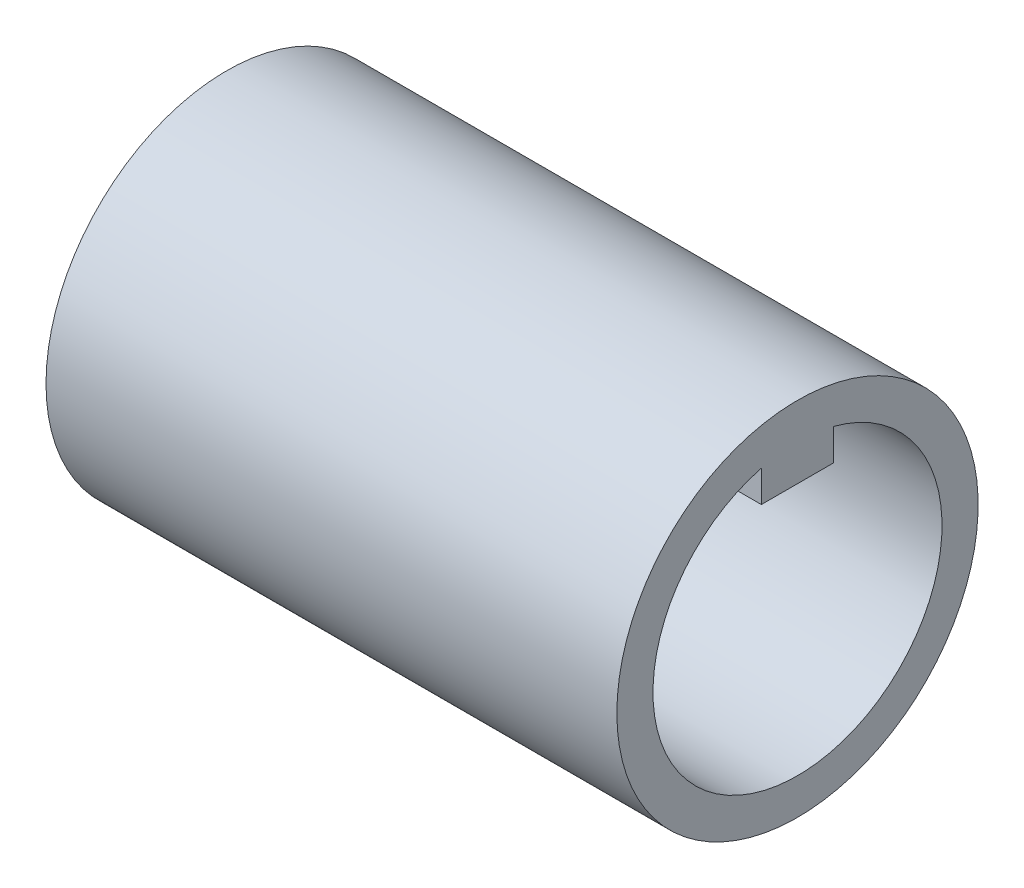
SolidWorks part; units mm, degrees
material "AISI 1020"
ref_plane "Спереди" through (0, 0, 0) normal (0, 0, 1) x (1, 0, 0)
ref_plane "Сверху" through (0, 0, 0) normal (0, 1, 0) x (1, 0, 0)
ref_plane "Справа" through (0, 0, 0) normal (1, 0, 0) x (0, 0, -1)
sketch "Эскиз1" plane through (0, 0, 0) normal (0, 1, 0) x (1, 0, 0)
  line L0 (-1000, 0) -> (49000, 0) construction
  line L1 (0, 10) -> (-35.5, 10)
  line L2 (-35.5, 10) -> (-35.5, 4.25)
  line L3 (-35.5, 4.25) -> (-39.5, 4.25)
  line L4 (-39.5, 4.25) -> (-39.5, 12.5)
  line L5 (-39.5, 12.5) -> (0, 12.5)
  line L6 (0, 12.5) -> (0, 10)
  line L7 (0, 22) -> (0, -22) construction
  line L8 (-35, 10) -> (-35, -10) construction
  line L9 (14, 10) -> (-35, 10) construction
  dimension "D1" = 0.5
  dimension "D2" = 25
  dimension "D3" = 4
  dimension "D4" = 8.5
revolve "Повернуть1" add sketch "Эскиз1" angle 360 about L0
sketch "Эскиз2" plane through (-39.5, 0, 0) normal (-1, 0, 0) x (0, 0, 1)
  line L0 (-2.5, 7.5) -> (2.5, 7.5) construction
  line L1 (-2.5, 7.5) -> (2.5, 7.5)
  line L2 (-2.5, 7.5) -> (-2.5, 10)
  line L3 (-2.5, 10) -> (2.5, 10)
  line L4 (2.5, 7.5) -> (2.5, 10)
  line L5 (2.5, 7.5) -> (2.5, 9.6825) construction
  circle A0 centre (0, 0) radius 10 construction
extrude "Бобышка-Вытянуть1" add sketch "Эскиз2" against normal up to surface (39.5 mm away) up to face at (0, 0, 12.5)
